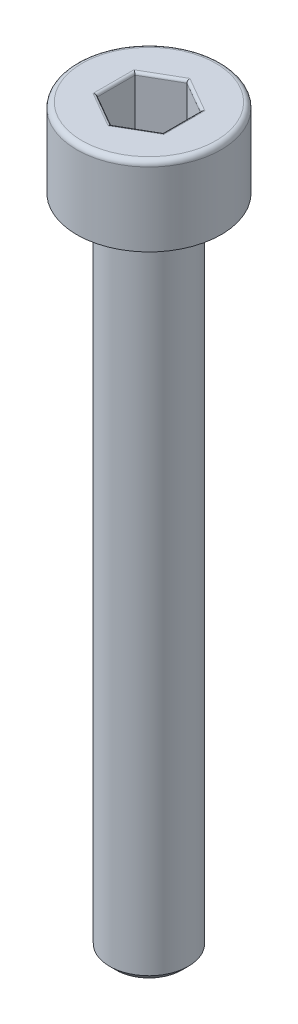
SolidWorks part; units mm, degrees
ref_plane "Front Plane" through (0, 0, 0) normal (0, 0, 1) x (1, 0, 0)
ref_plane "Top Plane" through (0, 0, 0) normal (0, 1, 0) x (1, 0, 0)
ref_plane "Right Plane" through (0, 0, 0) normal (1, 0, 0) x (0, 0, -1)
sketch "Sketch1" plane through (0, 0, 0) normal (0, 0, 1) x (1, 0, 0)
  line L0 (0, 0) -> (0, -47.0967) construction
  line L1 (0, -28) -> (-1.5, -28)
  line L2 (-1.5, -28) -> (-1.5, -3)
  line L3 (-1.5, -3) -> (-2.75, -3)
  line L4 (-2.75, -3) -> (-2.75, 0)
  line L5 (-2.75, 0) -> (0, 0)
  line L6 (0, 0) -> (0, -28)
  dimension "D1" = 25
  dimension "d" = 3
  dimension "k" = 3
  dimension "dk" = 5.5
revolve "Revolve1" add sketch "Sketch1" angle 360 about L0
chamfer "Chamfer1" distance 0.25 angle 45 2 edges at (0, -3, 1.5) (0, -28, 1.5)
fillet "Fillet1" radius 0.2 1 edges at (0, 0, 2.75)
sketch "Sketch2" plane through (0, 0, 0) normal (0, 1, 0) x (1, 0, 0)
  line L1 (0, 1.4434) -> (-1.25, 0.7217)
  line L2 (-1.25, 0.7217) -> (-1.25, -0.7217)
  line L3 (-1.25, -0.7217) -> (0, -1.4434)
  line L4 (0, -1.4434) -> (1.25, -0.7217)
  line L5 (1.25, -0.7217) -> (1.25, 0.7217)
  line L6 (1.25, 0.7217) -> (0, 1.4434)
  circle A0 centre (0, 0) radius 1.25 construction
  dimension "s" = 2.5
extrude "Cut-Extrude1" cut sketch "Sketch2" against normal blind 2
fillet "Fillet2" radius 0.1 12 edges at (-0.625, 0, -1.0825) (-1.25, 0, 0) (-0.625, 0, 1.0825) (0.625, 0, 1.0825) (1.25, 0, 0) (0.625, 0, -1.0825) (1.25, -2, 0) (0.625, -2, 1.0825) (-0.625, -2, 1.0825) (-1.25, -2, 0) (-0.625, -2, -1.0825) (0.625, -2, -1.0825)
